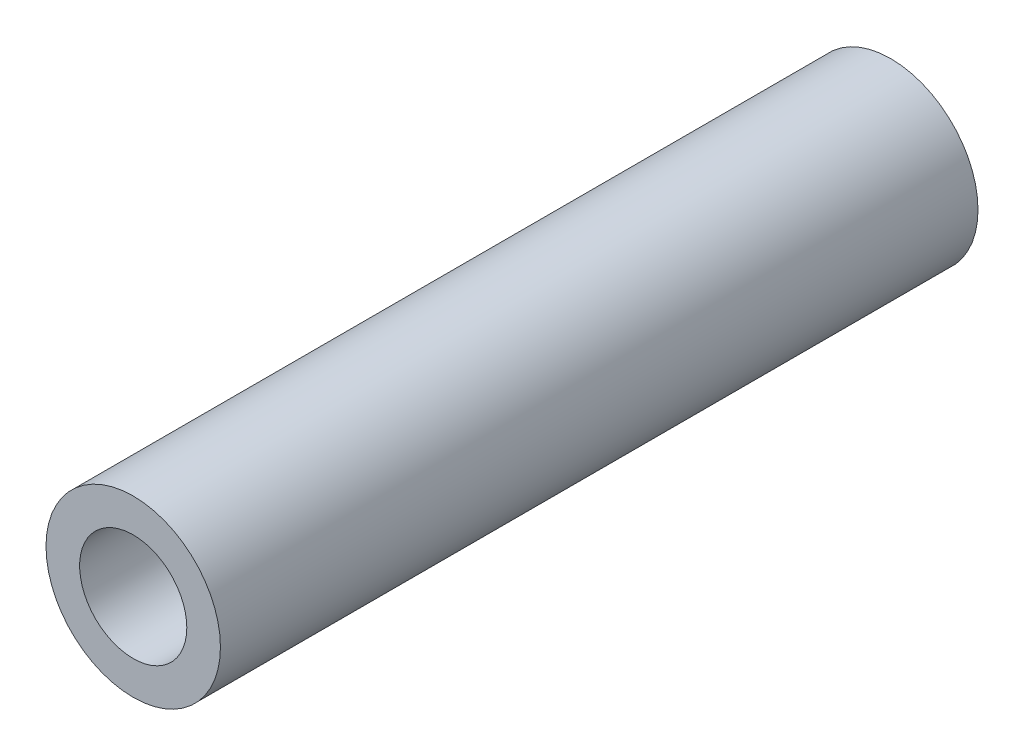
SolidWorks part; units mm, degrees
material "ABS"
ref_plane "前视基准面" through (0, 0, 0) normal (0, 0, 1) x (1, 0, 0)
ref_plane "上视基准面" through (0, 0, 0) normal (0, 1, 0) x (1, 0, 0)
ref_plane "右视基准面" through (0, 0, 0) normal (1, 0, 0) x (0, 0, -1)
sketch "草图1" plane through (0, 0, 0) normal (0, 0, 1) x (1, 0, 0)
  circle A1 centre (0, 0) radius 3.5
  circle A2 centre (0, 0) radius 2.15
  dimension "D1" = 7
  dimension "D2" = 4.3
extrude "凸台-拉伸1" add sketch "草图1" along normal blind 30.4
hole_wizard "M4 螺纹孔1" [suppressed] positions "草图2" profile "草图3" tap size "M4" standard "GB"
sketch "草图2" plane through (0, 0, 30.4) normal (0, 0, 1) x (1, 0, 0)
  point P0 (0, 0)
cosmetic thread "孔螺蚊线1" [suppressed] parameters "D2"=4
sketch "草图3" plane through (0, 0, 30.4) normal (1, 0, 0) x (0, -1, 0)
  line L0 (0, 0) -> (0, 30.4)
  line L1 (0, 30.4) -> (1.65, 30.4)
  line L2 (1.65, 30.4) -> (1.65, 0)
  line L5 (1.65, 0) -> (0, 0)
  line L11 (0, -6.35) -> (0, 107.95) construction
  dimension "通孔螺纹孔钻头直径" = 3.3
  dimension "通孔螺纹孔钻头深度" = 30.4
